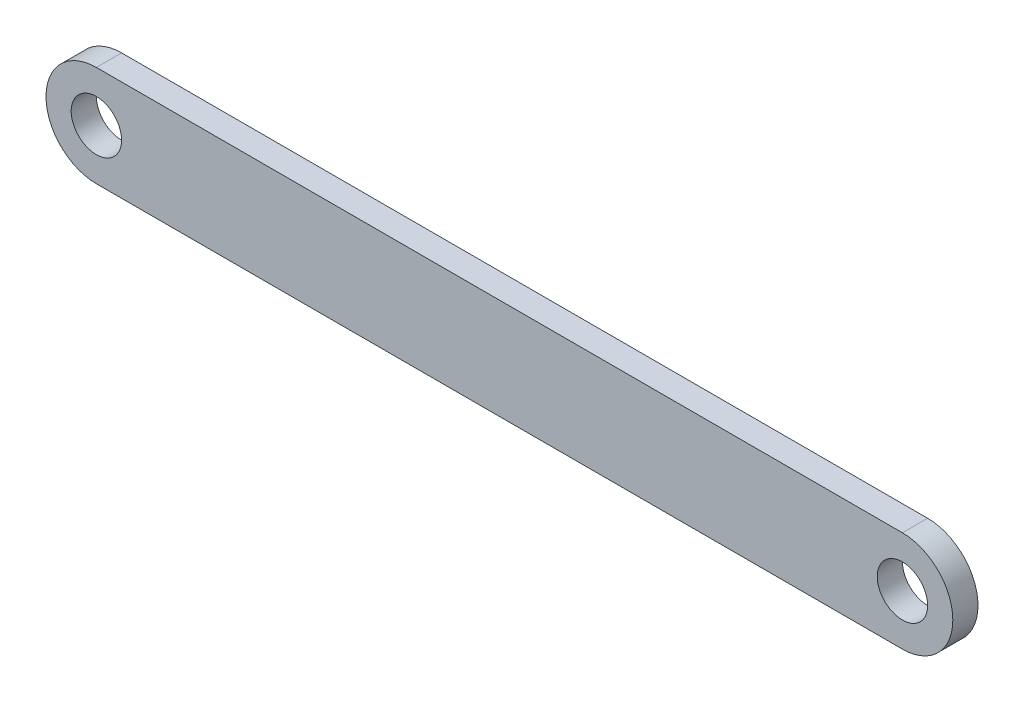
SolidWorks part; units mm, degrees
material "AISI 304"
ref_plane "Front" through (0, 0, 0) normal (0, 0, 1) x (1, 0, 0)
ref_plane "Top" through (0, 0, 0) normal (0, 1, 0) x (1, 0, 0)
ref_plane "Right" through (0, 0, 0) normal (1, 0, 0) x (0, 0, -1)
sketch "Sketch1" plane through (0, 0, 0) normal (0, 0, 1) x (1, 0, 0)
  line L0 (101.6, 12.7) -> (-101.6, -12.7) construction
  line L1 (-101.6, 12.7) -> (101.6, 12.7)
  line L2 (-101.6, 12.7) -> (-101.6, -12.7) construction
  line L3 (-101.6, -12.7) -> (101.6, -12.7)
  line L4 (101.6, 12.7) -> (101.6, -12.7) construction
  arc A0 (-101.6, -12.7) -> (-101.6, 12.7) centre (-101.6, 0) cw
  arc A1 (101.6, 12.7) -> (101.6, -12.7) centre (101.6, 0) cw
  dimension "D1" = 203.2
  dimension "D2" = 25.4
extrude "Extrude1" add sketch "Sketch1" along normal blind 6.35
sketch "Sketch5" plane through (0, 0, 6.35) normal (0, 0, 1) x (1, 0, 0)
  circle A0 centre (-101.6, 0) radius 6.35
  circle A1 centre (101.6, 0) radius 6.35
  dimension "D1" = 12.7
extrude "Cut-Extrude1" cut sketch "Sketch5" against normal through all
